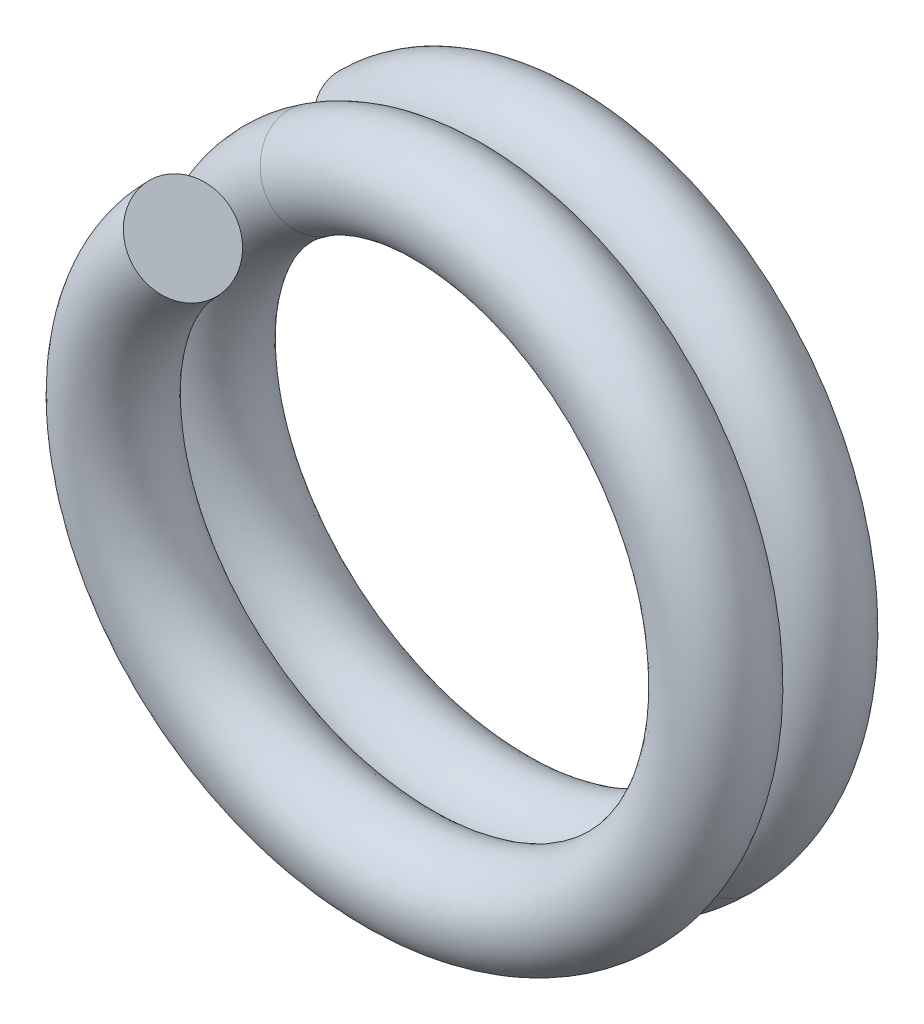
SolidWorks part; units mm, degrees
ref_plane "Front Plane" through (0, 0, 0) normal (0, 0, 1) x (1, 0, 0)
ref_plane "Top Plane" through (0, 0, 0) normal (0, 1, 0) x (1, 0, 0)
ref_plane "Right Plane" through (0, 0, 0) normal (1, 0, 0) x (0, 0, -1)
sketch "Sketch1" plane through (0, 0, 0) normal (0, 0, 1) x (1, 0, 0)
  line L1 (0, 0) -> (0, -111.0146) construction
  circle A0 centre (0, 0) radius 8.75
curve "Helix/Spiral1" pitch 3 height 6 turns 2
ref_plane "Plane5" through (-6.1872, 6.1872, 6) normal (0.7061, 0.7061, 0.0545) x (0.0385, 0.0385, -0.9985)
sketch "Sketch11" plane through (-6.1872, 6.1872, 6) normal (0.7061, 0.7061, 0.0545) x (0.0385, 0.0385, -0.9985)
  circle A1 centre (0.0154, 0.0033) radius 0.8
sweep "Sweep1" add path "Helix/Spiral1" circular profile diameter 3 parameters "D3"=3
